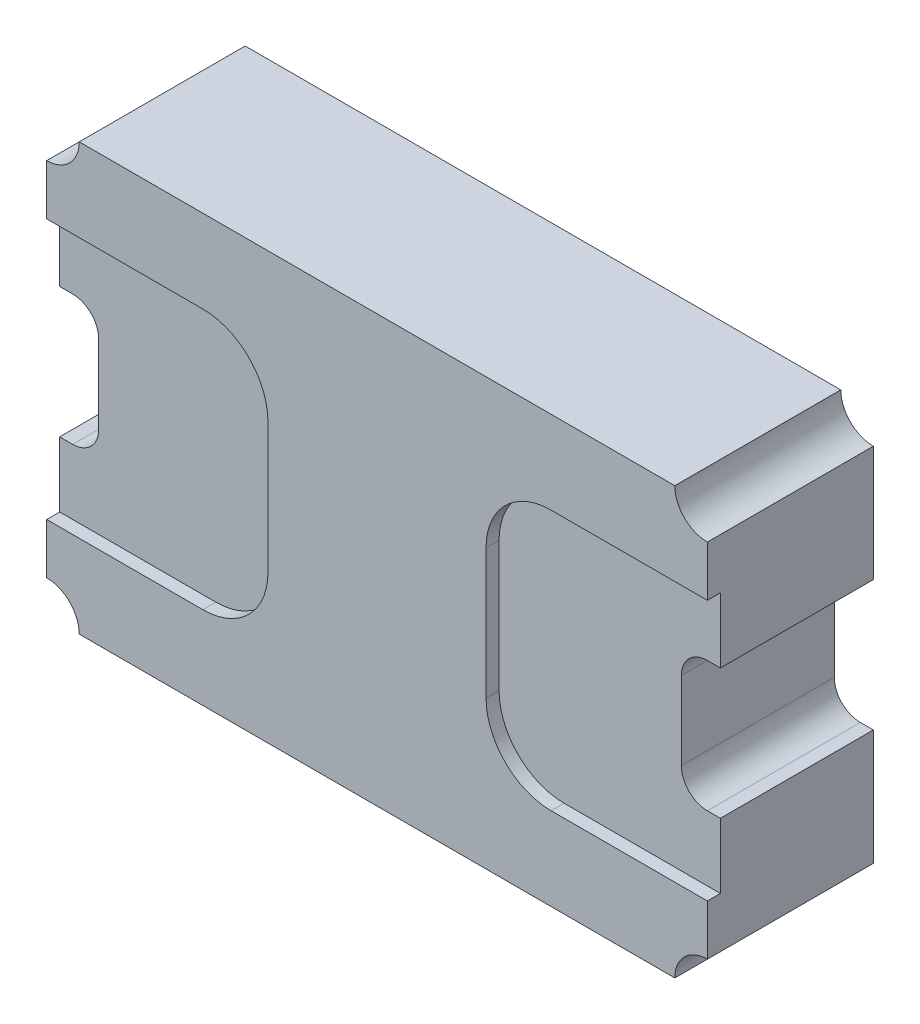
SolidWorks part; units mm, degrees
ref_plane "Ön Düzlem" through (0, 0, 0) normal (0, 0, 1) x (1, 0, 0)
ref_plane "Üst Düzlem" through (0, 0, 0) normal (0, 1, 0) x (1, 0, 0)
ref_plane "Sağ Düzlem" through (0, 0, 0) normal (1, 0, 0) x (0, 0, -1)
sketch "Çizim1" plane through (0, 0, 0) normal (0, 0, 1) x (1, 0, 0)
  line L1 (-2.5375, 1.6375) -> (2.5375, 1.6375)
  line L2 (-2.5375, 1.6375) -> (-2.5375, -1.6375)
  line L3 (-2.5375, -1.6375) -> (2.5375, -1.6375)
  line L4 (2.5375, 1.6375) -> (2.5375, -1.6375)
  line L5 (-2.5375, 1.6375) -> (2.5375, -1.6375) construction
  line L6 (-2.5375, -1.6375) -> (2.5375, 1.6375) construction
  point P0 (0, 0)
  dimension "D1" = 5.075
  dimension "D2" = 3.275
extrude "Yükseklik-Ekstrüzyon1" add sketch "Çizim1" along normal blind 1.275
sketch "Çizim2" plane through (2.5375, 0, 0) normal (1, 0, 0) x (0, 0, -1)
  line L0 (0, 0) -> (-1.275, 0) construction
  line L2 (-1.275, -1.6375) -> (-1.275, 1.6375) construction
  line L3 (-1.275, 1) -> (-1.275, -1)
  line L4 (-1.275, 1) -> (-1.175, 1)
  line L5 (-1.175, 1) -> (-1.175, -1)
  line L6 (-1.175, -1) -> (-1.275, -1)
  point P8 (-1.275, 0)
  dimension "D1" = 2
  dimension "D2" = 0.1
extrude "Kes-Ekstrüzyon1" cut sketch "Çizim2" against normal blind 1.7
sketch "Çizim3" plane through (-2.5375, 0, 0) normal (-1, 0, 0) x (0, 0, 1)
  line L0 (1.275, -1) -> (1.275, 1)
  line L1 (1.275, 1.6375) -> (1.275, -1.6375) construction
  line L2 (1.275, 1) -> (1.175, 1)
  line L3 (1.175, 1) -> (1.175, -1)
  line L4 (1.175, -1) -> (1.275, -1)
  point P5 (1.275, 0)
  dimension "D1" = 2
  dimension "D2" = 0.1
extrude "Kes-Ekstrüzyon2" cut sketch "Çizim3" against normal blind 1.7
sketch "Çizim4" plane through (0, 0, 0) normal (0, 0, -1) x (-1, 0, 0)
  line L0 (2.5375, 0) -> (2.2375, 0) construction
  line L1 (2.5375, 1.6375) -> (2.5375, -1.6375) construction
  line L2 (-2.5375, 0) -> (-2.2375, 0) construction
  line L3 (-2.5375, -1.6375) -> (-2.5375, 1.6375) construction
  line L4 (-2.2375, -0.3) -> (-2.2375, 0.3)
  line L5 (2.2375, -0.3) -> (2.2375, 0.3)
  line L6 (-2.4375, 0.5) -> (-2.5375, 0.5)
  line L7 (-2.4375, -0.5) -> (-2.5375, -0.5)
  line L8 (-2.5375, -0.5) -> (-2.5375, 0.5)
  line L9 (2.4375, 0.5) -> (2.5375, 0.5)
  line L10 (2.5375, 0.5) -> (2.5375, -0.5)
  line L11 (2.5375, -0.5) -> (2.4375, -0.5)
  arc A0 (2.2375, -0.3) -> (2.4375, -0.5) centre (2.4375, -0.3) ccw
  arc A1 (2.2375, 0.3) -> (2.4375, 0.5) centre (2.4375, 0.3) cw
  arc A2 (-2.2375, -0.3) -> (-2.4375, -0.5) centre (-2.4375, -0.3) cw
  arc A3 (-2.2375, 0.3) -> (-2.4375, 0.5) centre (-2.4375, 0.3) ccw
  point P12 (-2.2375, 0)
  point P15 (2.2375, 0)
  point P21 (2.2375, -0.5)
  point P24 (2.2375, 0.5)
  point P27 (-2.2375, -0.5)
  point P30 (-2.2375, 0.5)
  dimension "D5" = 0.2
  dimension "D1" = 0.3
  dimension "D2" = 0.3
  dimension "D3" = 1
  dimension "D4" = 1
extrude "Kes-Ekstrüzyon3" cut sketch "Çizim4" against normal blind 1.7
sketch "Çizim5" plane through (0, 0, 0) normal (0, 0, -1) x (-1, 0, 0)
  circle A0 centre (-2.5375, 1.6375) radius 0.25
  circle A1 centre (2.5375, 1.6375) radius 0.25
  circle A2 centre (2.5375, -1.6375) radius 0.25
  circle A3 centre (-2.5375, -1.6375) radius 0.25
  dimension "D1" = 0.5
extrude "Kes-Ekstrüzyon4" cut sketch "Çizim5" against normal blind 1.7
fillet "Radyus1" radius 0.5 4 edges at (-0.8375, 1, 1.225) (-0.8375, -1, 1.225) (0.8375, -1, 1.225) (0.8375, 1, 1.225)
